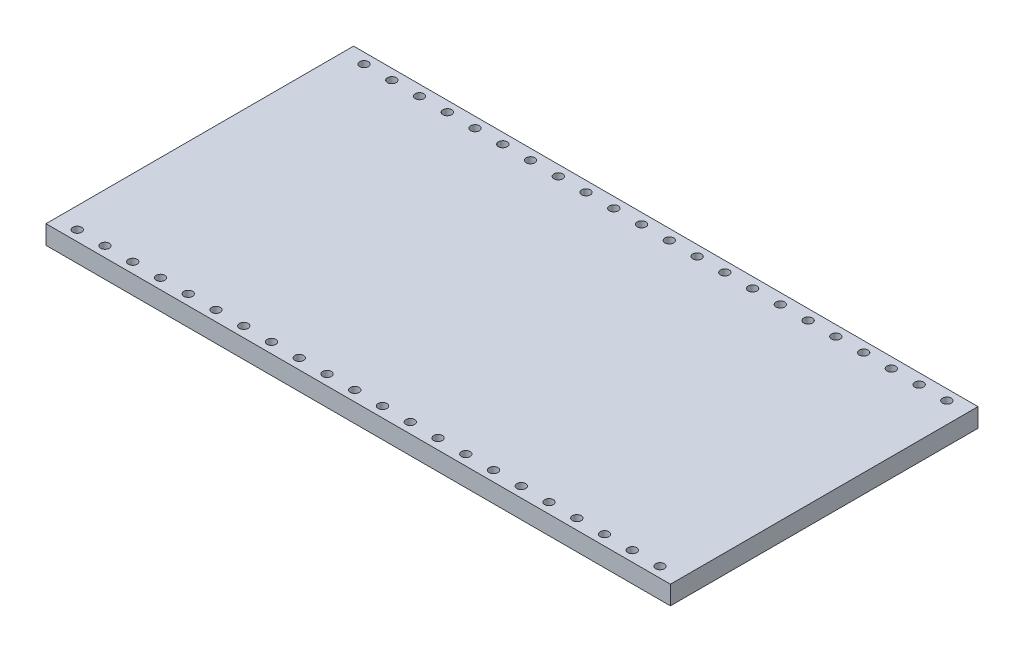
SolidWorks part; units mm, degrees
ref_plane "Front Plane" through (0, 0, 0) normal (0, 0, 1) x (1, 0, 0)
ref_plane "Top Plane" through (0, 0, 0) normal (0, 1, 0) x (1, 0, 0)
ref_plane "Right Plane" through (0, 0, 0) normal (1, 0, 0) x (0, 0, -1)
sketch "Sketch1" plane through (0, 0, 0) normal (0, 1, 0) x (1, 0, 0)
  line L1 (-28.575, -14.075) -> (28.575, -14.075)
  line L2 (-28.575, -14.075) -> (-28.575, 14.075)
  line L3 (-28.575, 14.075) -> (28.575, 14.075)
  line L4 (28.575, -14.075) -> (28.575, 14.075)
  line L5 (-28.575, -14.075) -> (28.575, 14.075) construction
  line L6 (-28.575, 14.075) -> (28.575, -14.075) construction
  point P0 (0, 0)
  dimension "D1" = 28.15
  dimension "D2" = 57.15
extrude "Boss-Extrude1" add sketch "Sketch1" along normal blind 1.72
sketch "Sketch2" plane through (0, 1.72, 0) normal (0, 1, 0) x (1, 0, 0)
  line L0 (28.575, 14.075) -> (-28.575, 14.075) construction
  line L1 (28.575, -14.075) -> (28.575, 14.075) construction
  circle A0 centre (26.675, 13.125) radius 0.4
  dimension "D1" = 0.8
  dimension "D2" = 0.95
  dimension "D3" = 1.9
extrude "Cut-Extrude1" cut sketch "Sketch2" against normal through all
pattern_linear "LPattern1" count 22 spacing 2.54 along (-1, 0, 0) of "Cut-Extrude1"
mirror "Mirror1" about plane through (0, 0, 0) normal (0, 0, 1) of "LPattern1", "Cut-Extrude1"
